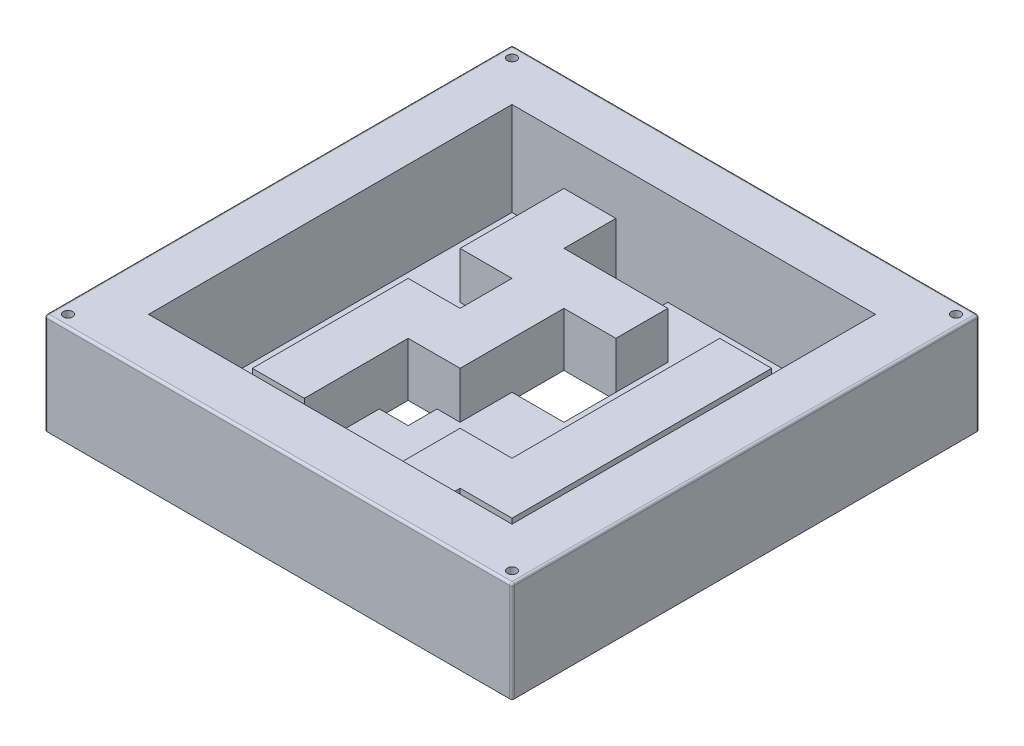
SolidWorks part; units mm, degrees
ref_plane "Plan de face" through (0, 0, 0) normal (0, 0, 1) x (1, 0, 0)
ref_plane "Plan de dessus" through (0, 0, 0) normal (0, 1, 0) x (1, 0, 0)
ref_plane "Plan de droite" through (0, 0, 0) normal (1, 0, 0) x (0, 0, -1)
sketch "Esquisse2" plane through (0, 0, 0) normal (0, 1, 0) x (1, 0, 0)
  line L1 (-100, 100) -> (100, 100)
  line L2 (-100, 100) -> (-100, -100)
  line L3 (-100, -100) -> (100, -100)
  line L4 (100, 100) -> (100, -100)
  dimension "D1" = 200
  dimension "D2" = 200
  dimension "D3" = 100
  dimension "D4" = 100
extrude "Boss.-Extru.1" add sketch "Esquisse2" against normal blind 3
sketch "Esquisse3" plane through (0, 0, 0) normal (0, 1, 0) x (1, 0, 0)
  line L0 (-77.77, 77.77) -> (77.77, 77.77)
  line L1 (-100, 100) -> (100, 100)
  line L2 (-100, 100) -> (-100, -100)
  line L3 (-100, -100) -> (100, -100)
  line L4 (100, 100) -> (100, -100)
  line L8 (77.77, 77.77) -> (77.77, -77.77)
  line L9 (-77.77, -77.77) -> (77.77, -77.77)
  line L10 (-77.77, 77.77) -> (-77.77, -77.77)
  dimension "D1" = 22.23
extrude "Boss.-Extru.2" add sketch "Esquisse3" along normal blind 40
sketch "Esquisse4" plane through (0, 0, 0) normal (0, 1, 0) x (1, 0, 0)
  line L0 (-55.55, 77.77) -> (-33.33, 77.77)
  line L1 (77.77, 77.77) -> (-77.77, 77.77) construction
  line L2 (-33.33, 77.77) -> (-33.33, 55.55)
  line L3 (-33.33, 55.55) -> (11.11, 55.55)
  line L4 (11.11, 55.55) -> (11.11, 33.33)
  line L5 (11.11, 33.33) -> (-11.11, 33.33)
  line L6 (-11.11, 33.33) -> (-11.11, -11.11)
  line L8 (-33.33, -11.11) -> (-33.33, -55.55)
  line L9 (-33.33, -55.55) -> (-55.55, -55.55)
  line L13 (-33.33, -11.11) -> (-11.11, -11.11)
  line L14 (-55.55, 77.77) -> (-55.55, 33.33)
  line L15 (-55.55, 33.33) -> (-33.33, 33.33)
  line L16 (-33.33, 33.33) -> (-33.33, 11.11)
  line L17 (-33.33, 11.11) -> (-55.55, 11.11)
  line L18 (-55.55, 11.11) -> (-55.55, -55.55)
  line L19 (-77.77, 77.77) -> (-77.77, -77.77) construction
  line L20 (-77.77, -77.77) -> (77.77, -77.77) construction
  line L21 (77.77, -77.77) -> (77.77, 77.77) construction
  line L22 (33.33, 55.55) -> (55.55, 55.55)
  line L23 (33.33, 55.55) -> (33.33, -33.33)
  line L25 (55.55, 55.55) -> (55.55, -55.55)
  line L28 (55.55, -55.55) -> (33.33, -55.55)
  line L30 (33.33, -33.33) -> (11.11, -33.33)
  line L32 (33.33, -77.77) -> (11.11, -77.77)
  line L33 (11.11, -33.33) -> (11.11, -77.77)
  line L34 (33.33, -55.55) -> (33.33, -77.77)
  line L35 (77.77, -77.77) -> (77.77, 77.77) construction
  dimension "D1" = 22.22
  dimension "D2" = 22.22
  dimension "D3" = 22.22
  dimension "D4" = 22.22
  dimension "D5" = 22.22
  dimension "D6" = 22.22
  dimension "D7" = 22.22
  dimension "D8" = 22.22
  dimension "D9" = 22.22
  dimension "D10" = 66.66
  dimension "D11" = 22.22
  dimension "D12" = 22.22
  dimension "D13" = 22.22
  dimension "D14" = 22.22
  dimension "D15" = 22.22
  dimension "D16" = 22.22
  dimension "D17" = 22.22
  dimension "D18" = 44.44
extrude "Boss.-Extru.3" add sketch "Esquisse4" along normal blind 20
sketch "Esquisse5" plane through (0, 0, 0) normal (0, 1, 0) x (1, 0, 0)
  line L0 (77.77, 77.77) -> (-33.33, 77.77) construction
  line L1 (-33.33, 55.55) -> (-11.11, 55.55)
  line L2 (-33.33, 55.55) -> (-33.33, 77.77)
  line L3 (-33.33, 77.77) -> (-11.11, 77.77)
  line L4 (-11.11, 55.55) -> (-11.11, 77.77)
  line L5 (-11.11, -11.11) -> (-11.11, 33.33) construction
  line L6 (-11.11, 33.33) -> (11.11, 33.33)
  line L7 (-11.11, 33.33) -> (-11.11, 11.11)
  line L8 (-11.11, 11.11) -> (11.11, 11.11)
  line L9 (11.11, 33.33) -> (11.11, 11.11)
  line L10 (11.11, 33.33) -> (11.11, 55.55) construction
  line L11 (-33.33, 11.11) -> (-55.55, 11.11) construction
  line L12 (33.33, -55.55) -> (55.55, -55.55) construction
  line L13 (-33.33, -11.11) -> (-20.98, -11.11)
  line L14 (-33.33, -11.11) -> (-33.33, -23.46)
  line L15 (-33.33, -23.46) -> (-20.98, -23.46)
  line L16 (-20.98, -11.11) -> (-20.98, -23.46)
  line L17 (-72.835, 28.395) -> (-60.485, 28.395)
  line L18 (-72.835, 28.395) -> (-72.835, 16.045)
  line L19 (-72.835, 16.045) -> (-60.485, 16.045)
  line L20 (-60.485, 28.395) -> (-60.485, 16.045)
  line L21 (-72.835, -60.485) -> (-60.485, -60.485)
  line L22 (-72.835, -60.485) -> (-72.835, -72.835)
  line L23 (-72.835, -72.835) -> (-60.485, -72.835)
  line L24 (-60.485, -60.485) -> (-60.485, -72.835)
  line L25 (60.485, -60.485) -> (72.835, -60.485)
  line L26 (60.485, -60.485) -> (60.485, -72.835)
  line L27 (60.485, -72.835) -> (72.835, -72.835)
  line L28 (72.835, -60.485) -> (72.835, -72.835)
  line L29 (11.11, -55.55) -> (-1.24, -55.55)
  line L30 (11.11, -55.55) -> (11.11, -43.2)
  line L31 (11.11, -43.2) -> (-1.24, -43.2)
  line L32 (-1.24, -55.55) -> (-1.24, -43.2)
  line L34 (11.11, -33.33) -> (11.11, -77.77) construction
  line L35 (-77.77, 77.77) -> (-77.77, -77.77) construction
  line L36 (-55.55, 33.33) -> (-33.33, 33.33) construction
  line L37 (-55.55, 77.77) -> (-55.55, 33.33) construction
  line L38 (-77.77, -77.77) -> (11.11, -77.77) construction
  line L39 (77.77, -77.77) -> (77.77, 77.77) construction
  dimension "D1" = 12.35
  dimension "D2" = 12.35
  dimension "D3" = 12.35
  dimension "D4" = 12.35
  dimension "D5" = 12.35
  dimension "D6" = 12.35
  dimension "D7" = 12.35
  dimension "D8" = 12.35
  dimension "D9" = 12.35
  dimension "D10" = 12.35
  dimension "D11" = 4.935
  dimension "D12" = 4.935
  dimension "D13" = 4.935
  dimension "D14" = 4.935
  dimension "D15" = 4.935
  dimension "D16" = 4.935
extrude "Enlèv. mat.-Extru.1" cut sketch "Esquisse5" against normal up to next
fillet "Congé1" radius 1 8 edges at (-100, 18.5, -100) (-100, 18.5, 100) (-100, 40, 0) (0, 40, 100) (0, 40, -100) (100, 40, 0) (100, 18.5, -100) (100, 18.5, 100)
sketch "Esquisse6" plane through (0, 40, 0) normal (0, 1, 0) x (1, 0, 0)
  line L0 (100, 99) -> (100, -99) construction
  line L1 (-99, 100) -> (99, 100) construction
  line L2 (99, -100) -> (-99, -100) construction
  line L3 (-100, -99) -> (-100, 99) construction
  circle A0 centre (-95, -95) radius 1
  circle A1 centre (95, -95) radius 1
  circle A2 centre (95, 95) radius 1
  circle A3 centre (-95, 95) radius 1
  point P8 (0, 0)
  point P13 (94.146, 96.2459)
  point P18 (0, 0)
  point P19 (0, 0)
  point P20 (0, 0)
  point P21 (0, 0)
  dimension "D1" = 2
  dimension "D2" = 5
  dimension "D3" = 5
  dimension "D4" = 5
  dimension "D5" = 5
extrude "Enlèv. mat.-Extru.2" cut sketch "Esquisse6" against normal through all
sketch "Esquisse7" plane through (0, 40, 0) normal (0, 1, 0) x (1, 0, 0)
  circle A0 centre (-95, -95) radius 2
  circle A1 centre (-95, 95) radius 2
  circle A2 centre (95, 95) radius 2
  circle A3 centre (95, -95) radius 2
  dimension "D1" = 4
extrude "Enlèv. mat.-Extru.3" cut sketch "Esquisse7" against normal blind 41
